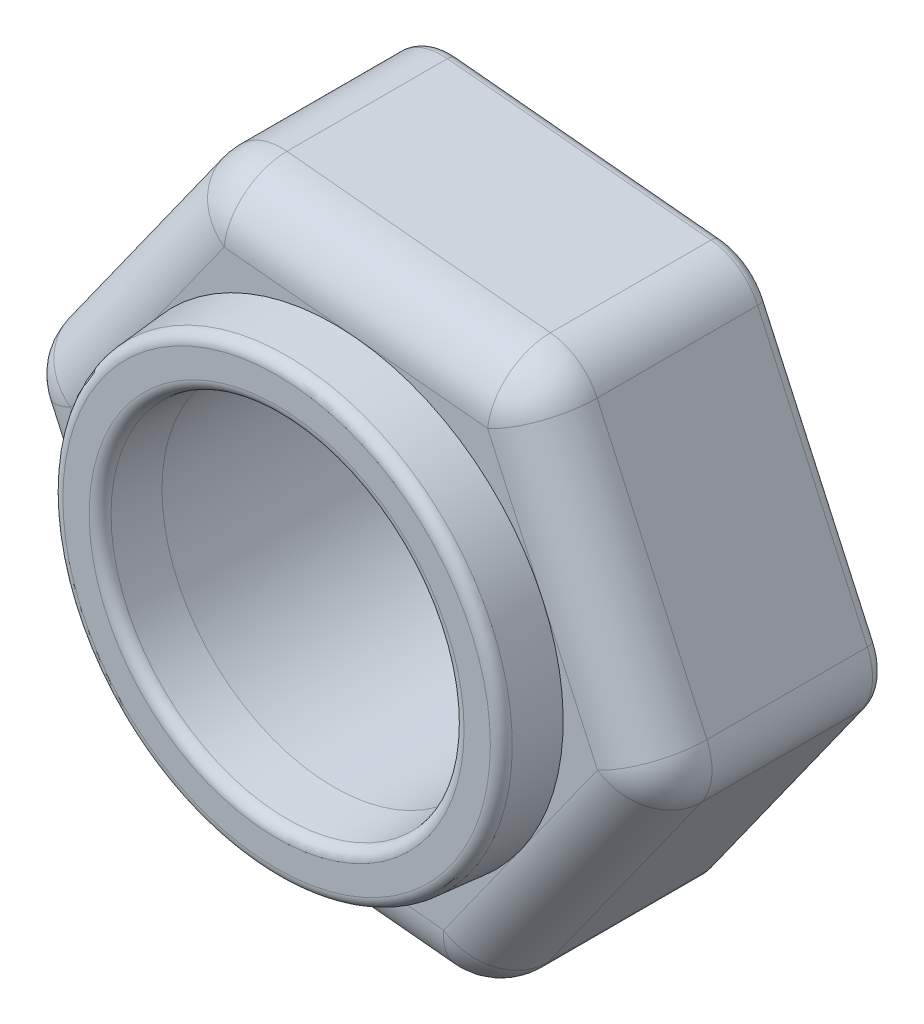
SolidWorks part; units mm, degrees
ref_plane "Ön Düzlem" through (0, 0, 0) normal (0, 0, 1) x (1, 0, 0)
ref_plane "Üst Düzlem" through (0, 0, 0) normal (0, 1, 0) x (1, 0, 0)
ref_plane "Sağ Düzlem" through (0, 0, 0) normal (1, 0, 0) x (0, 0, -1)
sketch "Sketch1" plane through (0, 0, 0) normal (0, 0, 1) x (1, 0, 0)
  line L2 (2.7538, -0.0137) -> (1.7958, 2.0877)
  line L3 (1.3887, 2.378) -> (-0.9101, 2.5991)
  line L4 (-1.365, 2.3916) -> (-2.7059, 0.5114)
  line L5 (-2.7538, 0.0137) -> (-1.7958, -2.0877)
  line L6 (-1.3887, -2.378) -> (0.9101, -2.5991)
  line L7 (1.365, -2.3916) -> (2.7059, -0.5114)
  circle A0 centre (0, 0) radius 1.5
  circle A1 centre (0, 0) radius 2.5 construction
  arc A2 (-1.7958, -2.0877) -> (-1.3887, -2.378) centre (-1.3408, -1.8803) ccw
  arc A3 (0.9101, -2.5991) -> (1.365, -2.3916) centre (0.958, -2.1013) ccw
  arc A4 (2.7538, -0.0137) -> (2.7059, -0.5114) centre (2.2988, -0.2211) cw
  arc A5 (1.7958, 2.0877) -> (1.3887, 2.378) centre (1.3408, 1.8803) ccw
  arc A6 (-0.9101, 2.5991) -> (-1.365, 2.3916) centre (-0.958, 2.1013) ccw
  arc A7 (-2.7059, 0.5114) -> (-2.7538, 0.0137) centre (-2.2988, 0.2211) ccw
  dimension "D1" = 3
  dimension "D3" = 0.5
  dimension "D2" = 5
extrude "Boss-Extrude1" add sketch "Sketch1" along normal blind 2
fillet "Fillet1" radius 0.5 12 edges at (1.6311, 2.2874, 2) (2.2748, 1.037, 2) (2.7965, -0.2689, 2) (2.0355, -1.4515, 2) (1.1654, -2.5563, 2) (-0.2393, -2.4885, 2) (-1.6311, -2.2874, 2) (-2.2748, -1.037, 2) (-2.7965, 0.2689, 2) (-2.0355, 1.4515, 2) (-1.1654, 2.5563, 2) (0.2393, 2.4885, 2)
sketch "Sketch3" plane through (0, 0, 2) normal (0, 0, 1) x (1, 0, 0)
  circle A0 centre (0, 0) radius 1.5
  circle A1 centre (0, 0) radius 2
  dimension "D1" = 4
extrude "Boss-Extrude2" add sketch "Sketch3" along normal blind 0.5 draft 5
fillet "Fillet2" radius 0.1 14 edges at (2.7965, -0.2689, 0) (2.0355, -1.4515, 0) (1.1654, -2.5563, 0) (-0.2393, -2.4885, 0) (-1.6311, -2.2874, 0) (-2.2748, -1.037, 0) (-2.7965, 0.2689, 0) (-2.0355, 1.4515, 0) (-1.1654, 2.5563, 0) (0.2393, 2.4885, 0) (1.6311, 2.2874, 0) (2.2748, 1.037, 0) (1.5437, 0, 2.5) (1.9563, 0, 2.5)
